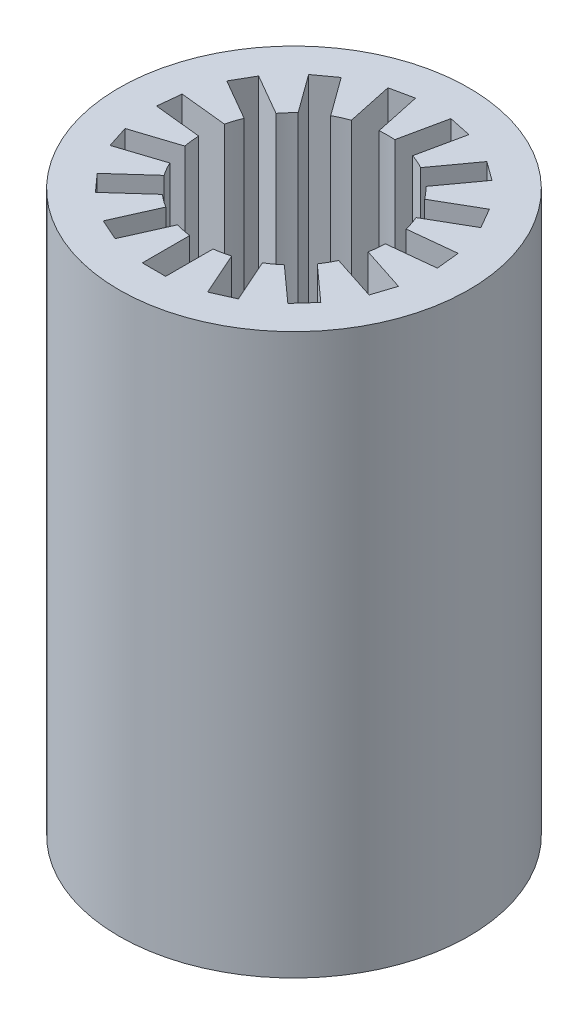
SolidWorks part; units mm, degrees
ref_plane "Front Plane" through (0, 0, 0) normal (0, 0, 1) x (1, 0, 0)
ref_plane "Top Plane" through (0, 0, 0) normal (0, 1, 0) x (1, 0, 0)
ref_plane "Right Plane" through (0, 0, 0) normal (1, 0, 0) x (0, 0, -1)
sketch "Sketch1" plane through (0, 0, 0) normal (0, 1, 0) x (1, 0, 0)
  line L0 (-0.5, -3.9686) -> (-0.5, -6)
  line L1 (-0.5, -6) -> (0.5, -6)
  line L2 (0.5, -6) -> (0.5, -3.9686)
  line L3 (0, 0) -> (0, -8.6414) construction
  line L4 (-2.071, -3.4222) -> (-2.8972, -5.2779)
  line L5 (-1.9836, -5.6846) -> (-1.1574, -3.8289)
  line L6 (-2.8972, -5.2779) -> (-1.9836, -5.6846)
  line L7 (-3.2838, -2.284) -> (-4.7934, -3.6432)
  line L8 (-4.1243, -4.3864) -> (-2.6147, -3.0271)
  line L9 (-4.7934, -3.6432) -> (-4.1243, -4.3864)
  line L10 (-3.9289, -0.7508) -> (-5.8608, -1.3786)
  line L11 (-5.5518, -2.3296) -> (-3.6199, -1.7019)
  line L12 (-5.8608, -1.3786) -> (-5.5518, -2.3296)
  line L13 (-3.8946, 0.9121) -> (-5.9149, 1.1244)
  line L14 (-6.0194, 0.1299) -> (-3.9992, -0.0824)
  line L15 (-5.9149, 1.1244) -> (-6.0194, 0.1299)
  line L16 (-3.1869, 2.4173) -> (-4.9462, 3.433)
  line L17 (-5.4462, 2.567) -> (-3.6869, 1.5513)
  line L18 (-4.9462, 3.433) -> (-5.4462, 2.567)
  line L19 (-1.9282, 3.5046) -> (-3.1222, 5.148)
  line L20 (-3.9312, 4.5602) -> (-2.7372, 2.9168)
  line L21 (-3.1222, 5.148) -> (-3.9312, 4.5602)
  line L22 (-0.3361, 3.9859) -> (-0.7584, 5.9728)
  line L23 (-1.7365, 5.7649) -> (-1.3142, 3.7779)
  line L24 (-0.7584, 5.9728) -> (-1.7365, 5.7649)
  line L25 (1.3142, 3.7779) -> (1.7365, 5.7649)
  line L26 (0.7584, 5.9728) -> (0.3361, 3.9859)
  line L27 (1.7365, 5.7649) -> (0.7584, 5.9728)
  line L28 (2.7372, 2.9168) -> (3.9312, 4.5602)
  line L29 (3.1222, 5.148) -> (1.9282, 3.5046)
  line L30 (3.9312, 4.5602) -> (3.1222, 5.148)
  line L31 (3.6869, 1.5513) -> (5.4462, 2.567)
  line L32 (4.9462, 3.433) -> (3.1869, 2.4173)
  line L33 (5.4462, 2.567) -> (4.9462, 3.433)
  line L34 (3.9992, -0.0824) -> (6.0194, 0.1299)
  line L35 (5.9149, 1.1244) -> (3.8946, 0.9121)
  line L36 (6.0194, 0.1299) -> (5.9149, 1.1244)
  line L37 (3.6199, -1.7019) -> (5.5518, -2.3296)
  line L38 (5.8608, -1.3786) -> (3.9289, -0.7508)
  line L39 (5.5518, -2.3296) -> (5.8608, -1.3786)
  line L40 (2.6147, -3.0271) -> (4.1243, -4.3864)
  line L41 (4.7934, -3.6432) -> (3.2838, -2.284)
  line L42 (4.1243, -4.3864) -> (4.7934, -3.6432)
  line L43 (1.1574, -3.8289) -> (1.9836, -5.6846)
  line L44 (2.8972, -5.2779) -> (2.071, -3.4222)
  line L45 (1.9836, -5.6846) -> (2.8972, -5.2779)
  arc A0 (0.5, -3.9686) -> (1.1574, -3.8289) centre (0, 0) ccw
  circle A1 centre (0, 0) radius 7.5
  arc A2 (2.071, -3.4222) -> (2.6147, -3.0271) centre (0, 0) ccw
  arc A3 (3.2838, -2.284) -> (3.6199, -1.7019) centre (0, 0) ccw
  arc A4 (3.9289, -0.7508) -> (3.9992, -0.0824) centre (0, 0) ccw
  arc A5 (3.8946, 0.9121) -> (3.6869, 1.5513) centre (0, 0) ccw
  arc A6 (3.1869, 2.4173) -> (2.7372, 2.9168) centre (0, 0) ccw
  arc A7 (1.9282, 3.5046) -> (1.3142, 3.7779) centre (0, 0) ccw
  arc A8 (0.3361, 3.9859) -> (-0.3361, 3.9859) centre (0, 0) ccw
  arc A9 (-1.3142, 3.7779) -> (-1.9282, 3.5046) centre (0, 0) ccw
  arc A10 (-2.7372, 2.9168) -> (-3.1869, 2.4173) centre (0, 0) ccw
  arc A11 (-3.6869, 1.5513) -> (-3.8946, 0.9121) centre (0, 0) ccw
  arc A12 (-3.9992, -0.0824) -> (-3.9289, -0.7508) centre (0, 0) ccw
  arc A13 (-3.6199, -1.7019) -> (-3.2838, -2.284) centre (0, 0) ccw
  arc A14 (-2.6147, -3.0271) -> (-2.071, -3.4222) centre (0, 0) ccw
  arc A15 (-1.1574, -3.8289) -> (-0.5, -3.9686) centre (0, 0) ccw
  point P10 (0, -6)
  point P14 (0, -4)
  point P69 (0, 0)
  dimension "D1" = 15
  dimension "D2" = 8
  dimension "D3" = 0
  dimension "D4" = 1
  dimension "D5" = 2
  dimension "D6" = 15
extrude "Boss-Extrude1" add sketch "Sketch1" along normal blind 24 contours A0 L43 L45 L44 A2 L40 L42 L41 A3 L37 L39 L38 A4 L34 L36 L35 A5 L31 L33 L32 A6 L28 L30 L29 A7 L25 L27 L26 A8 L22 L24 L23 A9 L19 L21 L20 A10 L16 L18 L17 A11 L13 L15 L14 A12 L10 L12 L11 A13 L7 L9 L8 A14 L4 L6 L5 A15 L0 L1 L2 | A1
